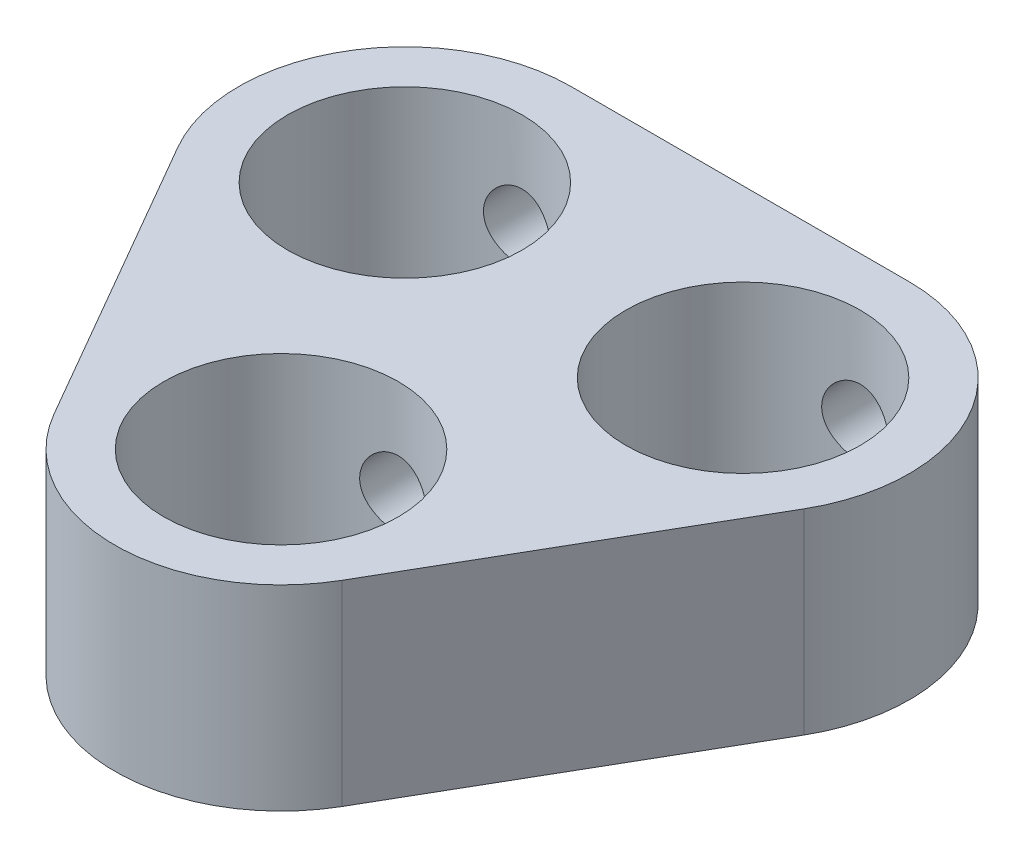
SolidWorks part; units mm, degrees
material "Chrome Stainless Steel"
ref_plane "Front Plane" through (0, 0, 0) normal (0, 0, 1) x (1, 0, 0)
ref_plane "Top Plane" through (0, 0, 0) normal (0, 1, 0) x (1, 0, 0)
ref_plane "Right Plane" through (0, 0, 0) normal (1, 0, 0) x (0, 0, -1)
sketch "Sketch1" plane through (0, 0, 0) normal (0, 1, 0) x (1, 0, 0)
  line L1 (-30.0083, 31.273) -> (33.9174, 31.273)
  line L2 (-30.0083, 31.273) -> (-30.0083, -24.6045)
  line L3 (-30.0083, -24.6045) -> (33.9174, -24.6045)
  line L4 (33.9174, 31.273) -> (33.9174, -24.6045)
extrude "Extrude1" add sketch "Sketch1" along normal blind 6.35
sketch "Sketch2" plane through (0, 0, 0) normal (0, -1, 0) x (1, 0, 0)
  line L0 (-10.1467, -0.4707) -> (-4.6657, 9.0227)
  line L1 (4.6657, 9.0227) -> (10.1467, -0.4707)
  line L2 (5.481, -8.552) -> (-5.481, -8.552)
  line L3 (0, 0) -> (7.4062, 4.276) construction
  circle A0 centre (0, 6.3289) radius 3.8
  circle A1 centre (5.481, -3.1645) radius 3.8
  circle A2 centre (-5.481, -3.1645) radius 3.8
  arc A3 (-5.481, -8.552) -> (-10.1467, -0.4707) centre (-5.481, -3.1645) cw
  arc A4 (-4.6657, 9.0227) -> (4.6657, 9.0227) centre (0, 6.3289) cw
  arc A5 (5.481, -8.552) -> (10.1467, -0.4707) centre (5.481, -3.1645) ccw
  dimension "D1" = 10.962
  dimension "D5" = 5.3875
  dimension "D6" = 5.3875
  dimension "D7" = 5.3875
  dimension "D2" = 10.962
  dimension "D3" = 10.962
  dimension "D4" = 5.481
extrude "Cut-Extrude1" cut sketch "Sketch2" against normal blind 6.35 flip side to cut
hole_wizard "#2-56 Tapped Hole1" positions "3DSketch1" profile "Sketch4" tap size "#2-56" standard "Ansi Inch"
sketch3d "3DSketch1"
  line L8 (-5.481, 6.35, -8.552) -> (-5.481, 0, -8.552) construction
  line L9 (5.481, 6.35, -8.552) -> (5.481, 0, -8.552) construction
  point P51 (5.481, 3.175, -8.552)
  point P53 (-5.481, 3.175, -8.552)
sketch "Sketch4" plane through (5.481, 3.175, -8.552) normal (1, 0, 0) x (0, 1, 0)
  line L0 (0, 0) -> (0, 6.1222)
  line L1 (0, 6.1222) -> (0.889, 5.588)
  line L2 (0.889, 5.588) -> (0.889, 4.318)
  line L3 (0.889, 4.318) -> (1.0922, 4.318)
  line L4 (1.0922, 4.318) -> (1.0922, 0)
  line L5 (1.0922, 0) -> (0, 0)
  line L10 (0, 6.1222) -> (-0.889, 5.588) construction
  line L11 (0, -6.35) -> (0, 107.95) construction
  dimension "Tap Drill Dia." = 1.778
  dimension "Tap Drill Depth" = 5.588
  dimension "Thread Major Dia." = 2.1844
  dimension "Thread Depth" = 4.318
  dimension "Drill Angle" = 118
hole_wizard "#2-56 Tapped Hole2" positions "3DSketch2" profile "Sketch5" tap size "#2-56" standard "Ansi Inch"
sketch3d "3DSketch2"
  line L0 (-4.6657, 6.35, 9.0227) -> (-10.1467, 6.35, -0.4707) construction
  line L1 (-5.481, 6.35, -8.552) -> (5.481, 6.35, -8.552) construction
  point P3 (-7.4062, 6.35, 4.276)
  point P9 (0, 3.175, -8.552)
  point P15 (0, 6.35, -8.552)
  dimension "D1" = 3.175
sketch "Sketch5" plane through (0, 3.175, -8.552) normal (1, 0, 0) x (0, 1, 0)
  line L0 (0, 0) -> (0, 13.7422)
  line L1 (0, 13.7422) -> (0.889, 13.208)
  line L2 (0.889, 13.208) -> (0.889, 11.938)
  line L3 (0.889, 11.938) -> (1.0922, 11.938)
  line L4 (1.0922, 11.938) -> (1.0922, 0)
  line L5 (1.0922, 0) -> (0, 0)
  line L10 (0, 13.7422) -> (-0.889, 13.208) construction
  line L11 (0, -6.35) -> (0, 107.95) construction
  dimension "Tap Drill Dia." = 1.778
  dimension "Tap Drill Depth" = 13.208
  dimension "Thread Major Dia." = 2.1844
  dimension "Thread Depth" = 11.938
  dimension "Drill Angle" = 118
